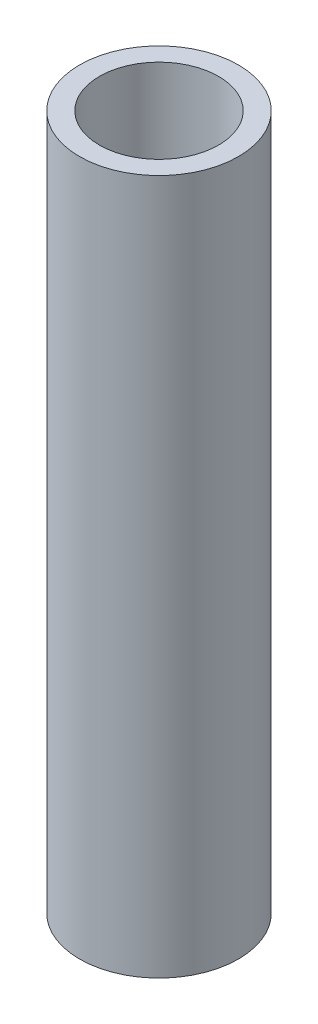
SolidWorks part; units mm, degrees
ref_plane "前视基准面" through (0, 0, 0) normal (0, 0, 1) x (1, 0, 0)
ref_plane "上视基准面" through (0, 0, 0) normal (0, 1, 0) x (1, 0, 0)
ref_plane "右视基准面" through (0, 0, 0) normal (1, 0, 0) x (0, 0, -1)
sketch "草图1" plane through (0, 0, 0) normal (0, 1, 0) x (1, 0, 0)
  circle A0 centre (0, 0) radius 6
  dimension "D1" = 12
extrude "拉伸-薄壁1" add sketch "草图1" against normal blind 70 thin
ref_plane "基准面4" through (0, -65, 0) normal (0, -1, 0) x (-1, 0, 0)
